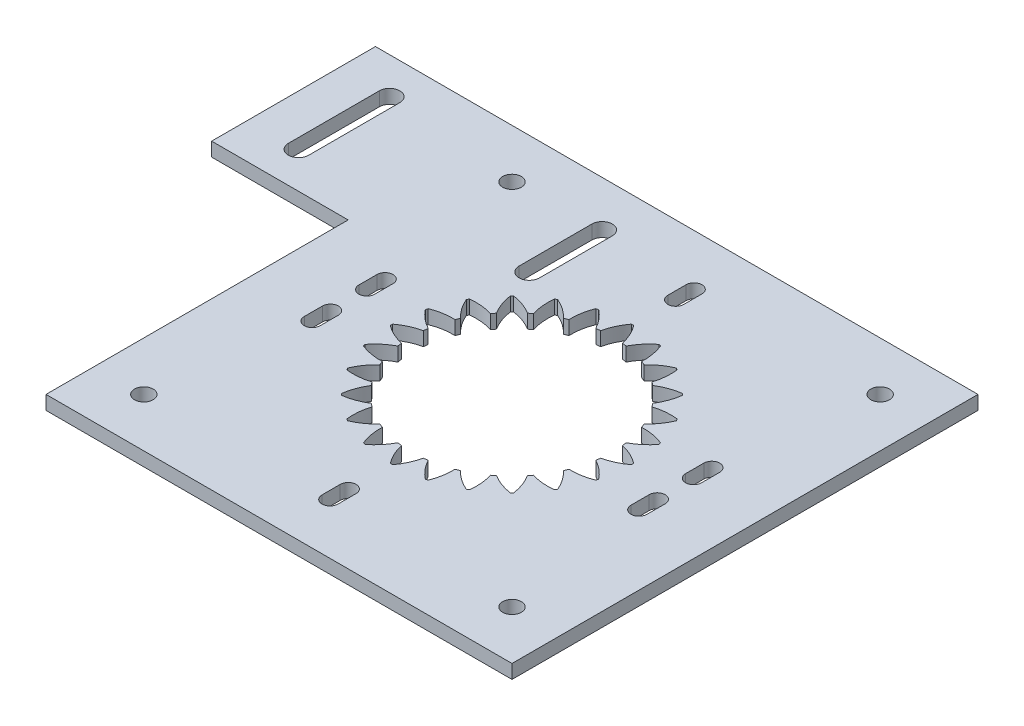
SolidWorks part; units mm, degrees
ref_plane "Front Plane" through (0, 0, 0) normal (0, 0, 1) x (1, 0, 0)
ref_plane "Top Plane" through (0, 0, 0) normal (0, 1, 0) x (1, 0, 0)
ref_plane "Right Plane" through (0, 0, 0) normal (1, 0, 0) x (0, 0, -1)
sketch "Sketch4" plane through (0, 0, 0) normal (0, 0, 1) x (1, 0, 0)
  line L0 (0, 0) -> (0, 40.0324) construction
sketch "Sketch1" plane through (0, 0, 0) normal (0, 1, 0) x (1, 0, 0)
  line L1 (-51.2, -51.2) -> (51.2, -51.2)
  line L2 (-51.2, -51.2) -> (-51.2, 15.2)
  line L3 (-51.2, 51.2) -> (51.2, 51.2)
  line L4 (51.2, -51.2) -> (51.2, 51.2)
  line L5 (-51.2, -51.2) -> (51.2, 51.2) construction
  line L6 (-51.2, 51.2) -> (51.2, -51.2) construction
  line L7 (-51.2, 51.2) -> (-81.2, 51.2)
  line L9 (-51.2, 15.2) -> (-81.2, 15.2)
  line L10 (-81.2, 51.2) -> (-81.2, 15.2)
  point P0 (0, 0)
  dimension "D1" = 102.4
  dimension "D2" = 102.4
  dimension "D3" = 30
  dimension "D4" = 36
extrude "Boss-Extrude1" add sketch "Sketch1" along normal blind 3.05
sketch "Sketch11" plane through (0, 3.05, 0) normal (0, 1, 0) x (1, 0, 0)
  arc B0 (6.6154, 25.662) -> (3.34, 21.745) centre (13.9727, 16.182) ccw
  arc B1 (7.1019, 25.5317) -> (6.6154, 25.662) centre (0, 0) ccw
  arc B2 (7.98, 20.5017) -> (7.1019, 25.5317) centre (-4.0097, 21.0004) ccw
  arc B3 (8.8542, 20.1396) -> (7.98, 20.5017) centre (0, 0) ccw
  arc B4 (13.0318, 23.0754) -> (8.8542, 20.1396) centre (17.6848, 12.0142) ccw
  arc B5 (13.468, 22.8236) -> (13.0318, 23.0754) centre (0, 0) ccw
  arc B6 (13.0143, 17.7378) -> (13.468, 22.8236) centre (1.5622, 21.3226) ccw
  arc B7 (13.765, 17.1617) -> (13.0143, 17.7378) centre (0, 0) ccw
  arc B8 (18.5601, 18.9163) -> (13.765, 17.1617) centre (20.1917, 7.0277) ccw
  arc B9 (18.9163, 18.5601) -> (18.5601, 18.9163) centre (0, 0) ccw
  arc B10 (17.1617, 13.765) -> (18.9163, 18.5601) centre (7.0277, 20.1917) ccw
  arc B11 (17.7378, 13.0143) -> (17.1617, 13.765) centre (0, 0) ccw
  arc B12 (22.8236, 13.468) -> (17.7378, 13.0143) centre (21.3226, 1.5622) ccw
  arc B13 (23.0754, 13.0318) -> (22.8236, 13.468) centre (0, 0) ccw
  arc B14 (20.1396, 8.8542) -> (23.0754, 13.0318) centre (12.0142, 17.6848) ccw
  arc B15 (20.5017, 7.98) -> (20.1396, 8.8542) centre (0, 0) ccw
  arc B16 (25.5317, 7.1019) -> (20.5017, 7.98) centre (21.0004, -4.0097) ccw
  arc B17 (25.662, 6.6154) -> (25.5317, 7.1019) centre (0, 0) ccw
  arc B18 (21.745, 3.34) -> (25.662, 6.6154) centre (16.182, 13.9727) ccw
  arc B19 (21.8685, 2.4018) -> (21.745, 3.34) centre (0, 0) ccw
  arc B20 (26.4998, 0.2518) -> (21.8685, 2.4018) centre (19.247, -9.3084) ccw
  arc B21 (26.4998, -0.2518) -> (26.4998, 0.2518) centre (0, 0) ccw
  arc B22 (21.8685, -2.4018) -> (26.4998, -0.2518) centre (19.247, 9.3084) ccw
  arc B23 (21.745, -3.34) -> (21.8685, -2.4018) centre (0, 0) ccw
  arc B24 (25.662, -6.6154) -> (21.745, -3.34) centre (16.182, -13.9727) ccw
  arc B25 (25.5317, -7.1019) -> (25.662, -6.6154) centre (0, 0) ccw
  arc B26 (20.5017, -7.98) -> (25.5317, -7.1019) centre (21.0004, 4.0097) ccw
  arc B27 (20.1396, -8.8542) -> (20.5017, -7.98) centre (0, 0) ccw
  arc B28 (23.0754, -13.0318) -> (20.1396, -8.8542) centre (12.0142, -17.6848) ccw
  arc B29 (22.8236, -13.468) -> (23.0754, -13.0318) centre (0, 0) ccw
  arc B30 (17.7378, -13.0143) -> (22.8236, -13.468) centre (21.3226, -1.5622) ccw
  arc B31 (17.1617, -13.765) -> (17.7378, -13.0143) centre (0, 0) ccw
  arc B32 (18.9163, -18.5601) -> (17.1617, -13.765) centre (7.0277, -20.1917) ccw
  arc B33 (18.5601, -18.9163) -> (18.9163, -18.5601) centre (0, 0) ccw
  arc B34 (13.765, -17.1617) -> (18.5601, -18.9163) centre (20.1917, -7.0277) ccw
  arc B35 (13.0143, -17.7378) -> (13.765, -17.1617) centre (0, 0) ccw
  arc B36 (13.468, -22.8236) -> (13.0143, -17.7378) centre (1.5622, -21.3226) ccw
  arc B37 (13.0318, -23.0754) -> (13.468, -22.8236) centre (0, 0) ccw
  arc B38 (8.8542, -20.1396) -> (13.0318, -23.0754) centre (17.6848, -12.0142) ccw
  arc B39 (7.98, -20.5017) -> (8.8542, -20.1396) centre (0, 0) ccw
  arc B40 (7.1019, -25.5317) -> (7.98, -20.5017) centre (-4.0097, -21.0004) ccw
  arc B41 (6.6154, -25.662) -> (7.1019, -25.5317) centre (0, 0) ccw
  arc B42 (3.34, -21.745) -> (6.6154, -25.662) centre (13.9727, -16.182) ccw
  arc B43 (2.4018, -21.8685) -> (3.34, -21.745) centre (0, 0) ccw
  arc B44 (0.2518, -26.4998) -> (2.4018, -21.8685) centre (-9.3084, -19.247) ccw
  arc B45 (-0.2518, -26.4998) -> (0.2518, -26.4998) centre (0, 0) ccw
  arc B46 (-2.4018, -21.8685) -> (-0.2518, -26.4998) centre (9.3084, -19.247) ccw
  arc B47 (-3.34, -21.745) -> (-2.4018, -21.8685) centre (0, 0) ccw
  arc B48 (-6.6154, -25.662) -> (-3.34, -21.745) centre (-13.9727, -16.182) ccw
  arc B49 (-7.1019, -25.5317) -> (-6.6154, -25.662) centre (0, 0) ccw
  arc B50 (-7.98, -20.5017) -> (-7.1019, -25.5317) centre (4.0097, -21.0004) ccw
  arc B51 (-8.8542, -20.1396) -> (-7.98, -20.5017) centre (0, 0) ccw
  arc B52 (-13.0318, -23.0754) -> (-8.8542, -20.1396) centre (-17.6848, -12.0142) ccw
  arc B53 (-13.468, -22.8236) -> (-13.0318, -23.0754) centre (0, 0) ccw
  arc B54 (-13.0143, -17.7378) -> (-13.468, -22.8236) centre (-1.5622, -21.3226) ccw
  arc B55 (-13.765, -17.1617) -> (-13.0143, -17.7378) centre (0, 0) ccw
  arc B56 (-18.5601, -18.9163) -> (-13.765, -17.1617) centre (-20.1917, -7.0277) ccw
  arc B57 (-18.9163, -18.5601) -> (-18.5601, -18.9163) centre (0, 0) ccw
  arc B58 (-17.1617, -13.765) -> (-18.9163, -18.5601) centre (-7.0277, -20.1917) ccw
  arc B59 (-17.7378, -13.0143) -> (-17.1617, -13.765) centre (0, 0) ccw
  arc B60 (-22.8236, -13.468) -> (-17.7378, -13.0143) centre (-21.3226, -1.5622) ccw
  arc B61 (-23.0754, -13.0318) -> (-22.8236, -13.468) centre (0, 0) ccw
  arc B62 (-20.1396, -8.8542) -> (-23.0754, -13.0318) centre (-12.0142, -17.6848) ccw
  arc B63 (-20.5017, -7.98) -> (-20.1396, -8.8542) centre (0, 0) ccw
  arc B64 (-25.5317, -7.1019) -> (-20.5017, -7.98) centre (-21.0004, 4.0097) ccw
  arc B65 (-25.662, -6.6154) -> (-25.5317, -7.1019) centre (0, 0) ccw
  arc B66 (-21.745, -3.34) -> (-25.662, -6.6154) centre (-16.182, -13.9727) ccw
  arc B67 (-21.8685, -2.4018) -> (-21.745, -3.34) centre (0, 0) ccw
  arc B68 (-26.4998, -0.2518) -> (-21.8685, -2.4018) centre (-19.247, 9.3084) ccw
  arc B69 (-26.4998, 0.2518) -> (-26.4998, -0.2518) centre (0, 0) ccw
  arc B70 (-21.8685, 2.4018) -> (-26.4998, 0.2518) centre (-19.247, -9.3084) ccw
  arc B71 (-21.745, 3.34) -> (-21.8685, 2.4018) centre (0, 0) ccw
  arc B72 (-25.662, 6.6154) -> (-21.745, 3.34) centre (-16.182, 13.9727) ccw
  arc B73 (-25.5317, 7.1019) -> (-25.662, 6.6154) centre (0, 0) ccw
  arc B74 (-20.5017, 7.98) -> (-25.5317, 7.1019) centre (-21.0004, -4.0097) ccw
  arc B75 (-20.1396, 8.8542) -> (-20.5017, 7.98) centre (0, 0) ccw
  arc B76 (-23.0754, 13.0318) -> (-20.1396, 8.8542) centre (-12.0142, 17.6848) ccw
  arc B77 (-22.8236, 13.468) -> (-23.0754, 13.0318) centre (0, 0) ccw
  arc B78 (-17.7378, 13.0143) -> (-22.8236, 13.468) centre (-21.3226, 1.5622) ccw
  arc B79 (-17.1617, 13.765) -> (-17.7378, 13.0143) centre (0, 0) ccw
  arc B80 (-18.9163, 18.5601) -> (-17.1617, 13.765) centre (-7.0277, 20.1917) ccw
  arc B81 (-18.5601, 18.9163) -> (-18.9163, 18.5601) centre (0, 0) ccw
  arc B82 (-13.765, 17.1617) -> (-18.5601, 18.9163) centre (-20.1917, 7.0277) ccw
  arc B83 (-13.0143, 17.7378) -> (-13.765, 17.1617) centre (0, 0) ccw
  arc B84 (-13.468, 22.8236) -> (-13.0143, 17.7378) centre (-1.5622, 21.3226) ccw
  arc B85 (-13.0318, 23.0754) -> (-13.468, 22.8236) centre (0, 0) ccw
  arc B86 (-8.8542, 20.1396) -> (-13.0318, 23.0754) centre (-17.6848, 12.0142) ccw
  arc B87 (-7.98, 20.5017) -> (-8.8542, 20.1396) centre (0, 0) ccw
  arc B88 (-7.1019, 25.5317) -> (-7.98, 20.5017) centre (4.0097, 21.0004) ccw
  arc B89 (-6.6154, 25.662) -> (-7.1019, 25.5317) centre (0, 0) ccw
  arc B90 (-3.34, 21.745) -> (-6.6154, 25.662) centre (-13.9727, 16.182) ccw
  arc B91 (-2.4018, 21.8685) -> (-3.34, 21.745) centre (0, 0) ccw
  arc B92 (-0.2518, 26.4998) -> (-2.4018, 21.8685) centre (9.3084, 19.247) ccw
  arc B93 (0.2518, 26.4998) -> (-0.2518, 26.4998) centre (0, 0) ccw
  arc B94 (2.4018, 21.8685) -> (0.2518, 26.4998) centre (-9.3084, 19.247) ccw
  arc B95 (3.34, 21.745) -> (2.4018, 21.8685) centre (0, 0) ccw
sketch_block_instance "Block2-1"
sketch_block "Block2"
extrude "Cut-Extrude6" cut sketch "Sketch11" against normal blind 10
sketch "Sketch3" plane through (0, 3.05, 0) normal (0, 1, 0) x (1, 0, 0)
  line L0 (51.2, -51.2) -> (51.2, 51.2) construction
  line L1 (51.2, 51.2) -> (-81.2, 51.2) construction
  circle A0 centre (40.45, 40.45) radius 2.05
  dimension "D3" = 4.1
  dimension "D1" = 10.75
  dimension "D2" = 10.75
extrude "Cut-Extrude2" cut sketch "Sketch3" against normal blind 10
pattern_circular "CirPattern1" count 4 over 360 about axis through (0, 0, 0) along (0, 1, 0) of "Cut-Extrude2"
sketch "Sketch7" plane through (0, 3.05, 0) normal (0, 1, 0) x (1, 0, 0)
  line L0 (-49.6947, 0) -> (47.5674, 0) construction
  line L1 (0, -37.2684) -> (0, -38.7316) construction
  line L2 (1.75, -37.2684) -> (1.75, -38.7316)
  line L3 (-1.75, -37.2684) -> (-1.75, -38.7316)
  line L4 (0, -40) -> (0, -36) construction
  line L5 (-1.75, -40) -> (-1.75, -36)
  line L6 (1.75, -40) -> (1.75, -36)
  arc A0 (1.75, -37.2684) -> (-1.75, -37.2684) centre (0, -37.2684) ccw
  arc A1 (-1.75, -38.7316) -> (1.75, -38.7316) centre (0, -38.7316) ccw
  arc A2 (-1.75, -40) -> (1.75, -40) centre (0, -40) ccw
  arc A3 (1.75, -36) -> (-1.75, -36) centre (0, -36) ccw
  point P5 (0, -38)
  point P12 (0, -38)
  dimension "D1" = 38
  dimension "D2" = 3.5
  dimension "D3" = 4
extrude "Cut-Extrude3" cut sketch "Sketch7" against normal up to surface (3.05 mm away) contours A3 L5 A2 L6 up to face at (40.45, 0, 38.4)
sketch "Sketch9" plane through (0, 3.05, 0) normal (0, 1, 0) x (1, 0, 0)
  line L0 (-54.2517, 0) -> (57.2543, 0) construction
  line L1 (35.9, -4) -> (35.9, -8) construction
  line L2 (37.65, -4) -> (37.65, -8)
  line L3 (34.15, -4) -> (34.15, -8)
  line L4 (51.2, -51.2) -> (51.2, 51.2) construction
  arc A0 (37.65, -4) -> (34.15, -4) centre (35.9, -4) ccw
  arc A1 (34.15, -8) -> (37.65, -8) centre (35.9, -8) ccw
  point P5 (35.9, -6)
  dimension "D3" = 15.3
  dimension "D1" = 3.5
  dimension "D2" = 4
  dimension "D4" = 6
extrude "Cut-Extrude4" cut sketch "Sketch9" against normal blind 10
mirror "Mirror1" about plane through (0, 0, 0) normal (1, 0, 0) of "Cut-Extrude4"
mirror "Mirror2" about plane through (0, 0, 0) normal (0, 0, 1) of "Cut-Extrude3", "Mirror1", "Cut-Extrude4"
sketch "Sketch10" plane through (0, 3.05, 0) normal (0, 1, 0) x (1, 0, 0)
  line L0 (-70.1, 43.2) -> (-70.1, 23.2) construction
  line L1 (-67.85, 43.2) -> (-67.85, 23.2)
  line L2 (-72.35, 43.2) -> (-72.35, 23.2)
  line L3 (51.2, 51.2) -> (-81.2, 51.2) construction
  line L4 (-21.4, 25.2) -> (-21.4, 41.2) construction
  line L5 (-23.65, 25.2) -> (-23.65, 41.2)
  line L6 (-19.15, 25.2) -> (-19.15, 41.2)
  arc A0 (-67.85, 43.2) -> (-72.35, 43.2) centre (-70.1, 43.2) ccw
  arc A1 (-72.35, 23.2) -> (-67.85, 23.2) centre (-70.1, 23.2) ccw
  arc A2 (-23.65, 25.2) -> (-19.15, 25.2) centre (-21.4, 25.2) ccw
  arc A3 (-19.15, 41.2) -> (-23.65, 41.2) centre (-21.4, 41.2) ccw
  point P2 (-70.1, 33.2)
  point P12 (-21.4, 33.2)
  dimension "D1" = 4.5
  dimension "D2" = 20
  dimension "D3" = 70.1
  dimension "D4" = 18
  dimension "D5" = 4.5
  dimension "D6" = 16
  dimension "D7" = 48.7
extrude "Cut-Extrude5" cut sketch "Sketch10" against normal blind 10
